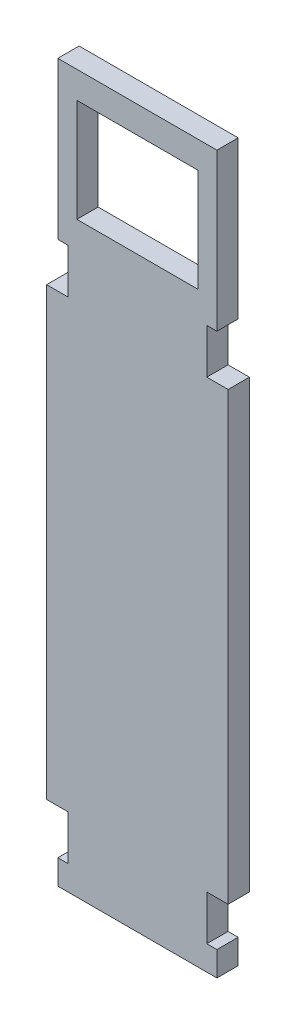
SolidWorks part; units mm, degrees
ref_plane "Front Plane" through (0, 0, 0) normal (0, 0, 1) x (1, 0, 0)
ref_plane "Top Plane" through (0, 0, 0) normal (0, 1, 0) x (1, 0, 0)
ref_plane "Right Plane" through (0, 0, 0) normal (1, 0, 0) x (0, 0, -1)
sketch "Sketch1" plane through (0, 0, 0) normal (0, 0, 1) x (1, 0, 0)
  line L0 (15.5, 154.5) -> (15.5, -5.5) construction
  line L2 (-4.75, 10) -> (-4.75, 109.5)
  line L4 (35.75, 10) -> (35.75, 109.5)
  line L7 (-4.75, 109.5) -> (0, 109.5)
  line L8 (0, 119.5) -> (0, 109.5)
  line L11 (-4.75, 10) -> (0, 10)
  line L12 (0, 0) -> (0, 10)
  line L13 (35.75, 10) -> (31, 10)
  line L14 (31, 0) -> (31, 10)
  line L17 (35.75, 109.5) -> (31, 109.5)
  line L18 (31, 119.5) -> (31, 109.5)
  line L21 (0, 119.5) -> (-2.25, 119.5)
  line L22 (33.25, 119.5) -> (31, 119.5)
  line L23 (33.25, 119.5) -> (33.25, 154.5)
  line L24 (33.25, 154.5) -> (-2.25, 154.5)
  line L25 (-2.25, 119.5) -> (-2.25, 154.5)
  line L26 (33.25, 0) -> (31, 0)
  line L27 (33.25, 0) -> (33.25, -5.5)
  line L28 (33.25, -5.5) -> (-2.25, -5.5)
  line L29 (-2.25, 0) -> (-2.25, -5.5)
  line L30 (0, 0) -> (-2.25, 0)
  line L32 (2, 125.5) -> (29, 125.5)
  line L33 (2, 125.5) -> (2, 148.5)
  line L34 (2, 148.5) -> (29, 148.5)
  line L35 (29, 125.5) -> (29, 148.5)
  line L36 (2, 125.5) -> (29, 148.5) construction
  line L37 (2, 148.5) -> (29, 125.5) construction
  point P24 (15.5, 137)
  point P30 (-2.25, 137)
  dimension "D1" = 31
  dimension "D2" = 99.5
  dimension "D3" = 4.75
  dimension "D4" = 10
  dimension "D5" = 160
  dimension "D6" = 27
  dimension "D7" = 23
  dimension "D8" = 35
  dimension "D9" = 35.5
  dimension "D10" = 35.5
extrude "Boss-Extrude1" add sketch "Sketch1" along normal blind 4.75
